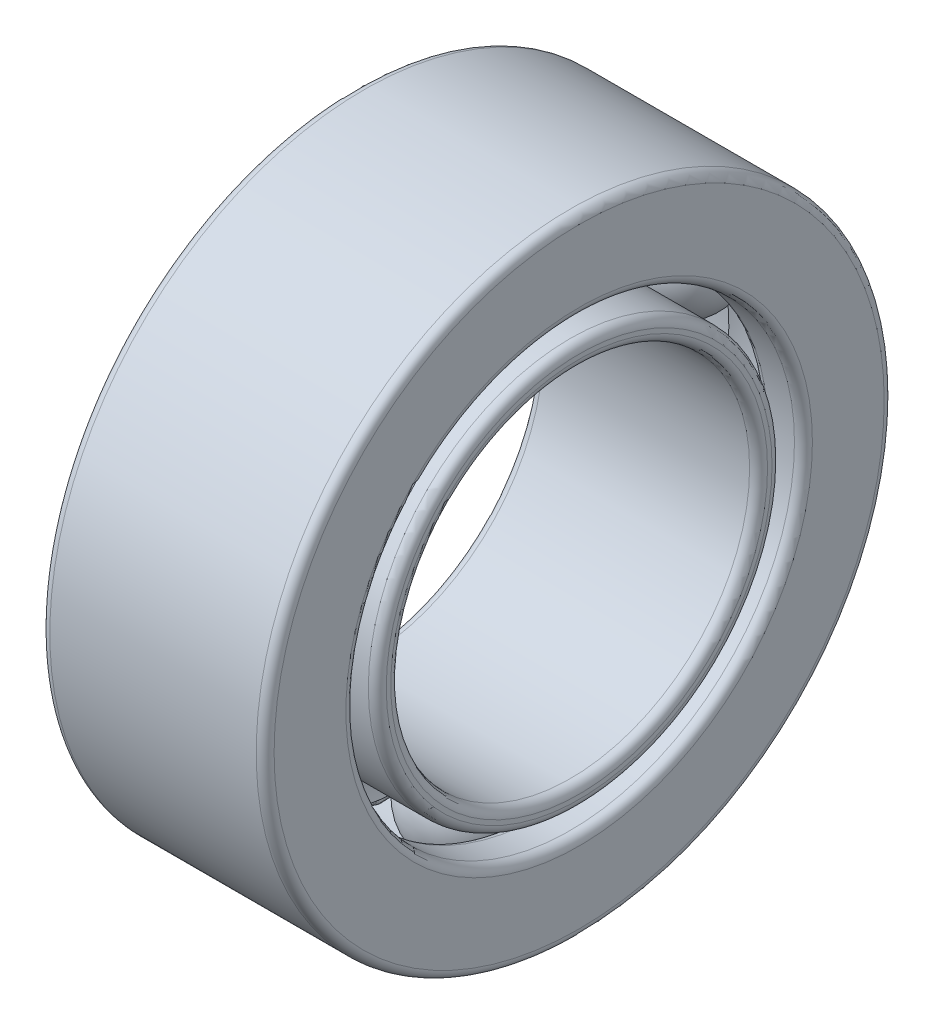
SolidWorks part; units mm, degrees
material "AISI 321 Annealed Stainless Steel (SS)"
ref_plane "Front Plane" through (0, 0, 0) normal (0, 0, 1) x (1, 0, 0)
ref_plane "Top Plane" through (0, 0, 0) normal (0, 1, 0) x (1, 0, 0)
ref_plane "Right Plane" through (0, 0, 0) normal (1, 0, 0) x (0, 0, -1)
sketch "Sketch1" plane through (0, 0, 0) normal (1, 0, 0) x (0, 0, -1)
  circle A0 centre (0, 0) radius 2
  circle A1 centre (0, 0) radius 3.5
  circle A2 centre (0, 0) radius 2.25
  circle A3 centre (0, 0) radius 3.25
  dimension "D1" = 4
  dimension "D2" = 7
  dimension "D3" = 4.5
  dimension "D4" = 6.5
extrude "Boss-Extrude1" add sketch "Sketch1" along normal mid plane 2.5 contours A1 A3 | A2 A0
sketch "Sketch2" plane through (0, 0, 0) normal (0, 0, 1) x (1, 0, 0)
  line L0 (0.3317, 2.25) -> (-0.3317, 2.25) construction
  line L1 (0.3317, 3.25) -> (-0.3317, 3.25) construction
  line L2 (0, 0) -> (2.2241, 0) construction
  line L4 (0.3317, 3.25) -> (-0.3317, 3.25)
  line L5 (0.3317, 2.25) -> (-0.3317, 2.25)
  arc A0 (-0.3317, 2.25) -> (0.3317, 2.25) centre (0, 2.75) ccw
  arc A1 (0.3317, 3.25) -> (-0.3317, 3.25) centre (0, 2.75) ccw
  dimension "D1" = 1.2
revolve "Cut-Revolve1" cut sketch "Sketch2" angle 360 about L2
sketch "Sketch3" plane through (0, 0, 0) normal (1, 0, 0) x (0, 0, -1)
  line L0 (0, 0) -> (0, 2.75) construction
  line L1 (0, 2.15) -> (0, 3.35)
  line L5 (0, -2.15) -> (0, -3.35)
  line L9 (-1.5203, -1.5203) -> (-2.3688, -2.3688) [skipped]
  line L10 (-2.15, 0) -> (-3.35, 0) [skipped]
  line L11 (-1.5203, 1.5203) -> (-2.3688, 2.3688) [skipped]
  line L12 (1.5203, 1.5203) -> (2.3688, 2.3688) [skipped]
  line L13 (2.15, 0) -> (3.35, 0) [skipped]
  line L14 (1.5203, -1.5203) -> (2.3688, -2.3688) [skipped]
  arc A0 (0, 2.15) -> (0, 3.35) centre (0, 2.75) ccw
  arc A4 (0, -2.15) -> (0, -3.35) centre (0, -2.75) ccw
  arc A8 (-1.5203, -1.5203) -> (-2.3688, -2.3688) centre (-1.9445, -1.9445) ccw [skipped]
  arc A9 (-2.15, 0) -> (-3.35, 0) centre (-2.75, 0) ccw [skipped]
  arc A10 (-1.5203, 1.5203) -> (-2.3688, 2.3688) centre (-1.9445, 1.9445) ccw [skipped]
  arc A11 (1.5203, 1.5203) -> (2.3688, 2.3688) centre (1.9445, 1.9445) ccw [skipped]
  arc A12 (2.15, 0) -> (3.35, 0) centre (2.75, 0) ccw [skipped]
  arc A13 (1.5203, -1.5203) -> (2.3688, -2.3688) centre (1.9445, -1.9445) ccw [skipped]
  point P29 (0, 0)
  dimension "D2" = 1.2
  dimension "D3" = 8
revolve "Revolve1" add sketch "Sketch3" angle 360 about L0
sketch "Sketch4" plane through (0, 0, 0) normal (1, 0, 0) x (0, 0, -1)
  line L1 (1.862, 1.075) -> (2.9012, 1.675)
  line L4 (-1.862, -1.075) -> (-2.9012, -1.675)
  arc A1 (1.862, 1.075) -> (2.9012, 1.675) centre (2.3816, 1.375) ccw
  arc A2 (-1.862, -1.075) -> (-2.9012, -1.675) centre (-2.3816, -1.375) ccw
  dimension "D3" = 1.2
revolve "Revolve2" add sketch "Sketch4" angle 360 about L4
sketch "Sketch5" plane through (0, 0, 0) normal (1, 0, 0) x (0, 0, -1)
  line L1 (-1.862, 1.075) -> (-2.3816, 1.375)
  line L2 (-1.862, 1.075) -> (-2.9012, 1.675)
  line L6 (1.862, -1.075) -> (2.3816, -1.375)
  line L7 (1.862, -1.075) -> (2.9012, -1.675)
  arc A0 (-1.862, 1.075) -> (-2.9012, 1.675) centre (-2.3816, 1.375) ccw
  arc A2 (1.862, -1.075) -> (2.9012, -1.675) centre (2.3816, -1.375) ccw
  dimension "D3" = 1.2
revolve "Revolve3" add sketch "Sketch5" angle 360 about L2
sketch "Sketch7" plane through (0, 0, 0) normal (0, 0, 1) x (1, 0, 0)
  line L0 (0, 0) -> (2.9907, 0) construction
  line L1 (1.25, 3.5) -> (0.75, 3.5)
  line L2 (1.25, 3.5) -> (1.25, 2.5)
  line L3 (1.25, 2.5) -> (0.75, 2.5)
  line L4 (0.75, 3.5) -> (0.75, 2.5)
  dimension "D1" = 0.5
  dimension "D2" = 1
revolve "Revolve5" add sketch "Sketch7" angle 360 about L0
sketch "Sketch8" plane through (0, 0, 0) normal (0, 0, 1) x (1, 0, 0)
  line L0 (0, 0) -> (-1.7035, 0) construction
  line L4 (-1.15, 2.75) -> (-1.15, 3)
  line L5 (-1.15, 2.75) -> (-1.15, 2.5)
  line L6 (-1.15, 3) -> (-0.6, 3)
  line L7 (-1.15, 2.5) -> (-0.6, 2.5)
  arc A0 (-0.6, 3) -> (-0.6, 2.5) centre (0, 2.75) ccw
  dimension "D2" = 1.3
  dimension "D4" = 0.25
  dimension "D5" = 0.25
revolve "Revolve6" add sketch "Sketch8" angle 360 about L0
fillet "Fillet1" radius 0.1 6 edges at (1.25, 0, 2.5) (0.75, 0, 2.5) (-1.25, 0, -3.25) (0.75, 0, -3.25) (-1.25, 0, -3.5) (1.25, 0, -3.5)
fillet "Fillet2" radius 0.1 4 edges at (1.25, 0, -2) (1.25, 0, -2.25) (-1.25, 0, -2) (-1.25, 0, -2.25)
fillet "Fillet3" radius 0.05 4 edges at (-0.6, 0, -3) (-0.6, 0, -2.5) (-1.15, 0, -2.5) (-1.15, 0, -3)
